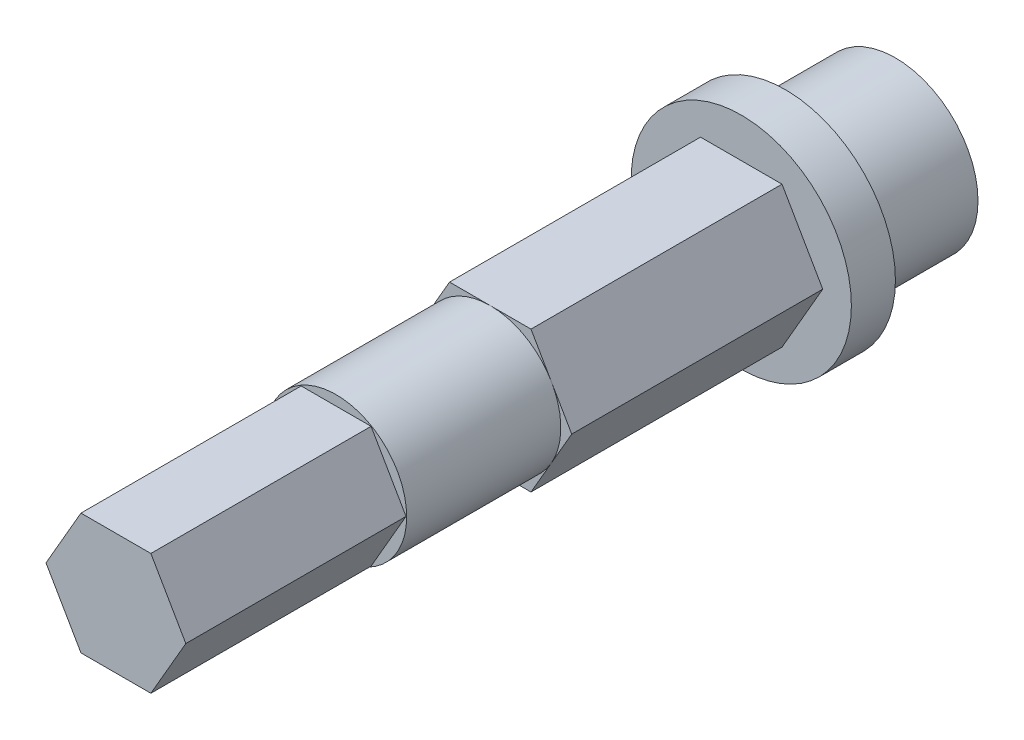
SolidWorks part; units mm, degrees
ref_plane "Front Plane" through (0, 0, 0) normal (0, 0, 1) x (1, 0, 0)
ref_plane "Top Plane" through (0, 0, 0) normal (0, 1, 0) x (1, 0, 0)
ref_plane "Right Plane" through (0, 0, 0) normal (1, 0, 0) x (0, 0, -1)
sketch "Sketch1" plane through (0, 0, 0) normal (0, 0, 1) x (1, 0, 0)
  circle A0 centre (0, 0) radius 3.75
  dimension "D1" = 7.5
extrude "Boss-Extrude1" add sketch "Sketch1" along normal blind 5
sketch "Sketch2" plane through (0, 0, 5) normal (0, 0, 1) x (1, 0, 0)
  circle A0 centre (0, 0) radius 5
  dimension "D1" = 10
extrude "Boss-Extrude2" add sketch "Sketch2" along normal blind 2
sketch "Sketch3" plane through (0, 0, 7) normal (0, 0, 1) x (1, 0, 0)
  line L7 (3.7, 0) -> (1.85, 3.2043)
  line L8 (1.85, 3.2043) -> (-1.85, 3.2043)
  line L9 (-1.85, 3.2043) -> (-3.7, 0)
  line L10 (-3.7, 0) -> (-1.85, -3.2043)
  line L11 (-1.85, -3.2043) -> (1.85, -3.2043)
  line L12 (1.85, -3.2043) -> (3.7, 0)
  circle A0 centre (0, 0) radius 3.7 construction
  circle A1 centre (0, 0) radius 3.2043 construction
  dimension "D1" = 7.4
extrude "Boss-Extrude3" add sketch "Sketch3" along normal blind 11.4
sketch "Sketch4" plane through (0, 0, 18.4) normal (0, 0, 1) x (1, 0, 0)
  line L2 (-1.85, 3.2043) -> (-3.7, 0) construction
  circle A0 centre (0, 0) radius 3.2043
extrude "Boss-Extrude4" add sketch "Sketch4" along normal blind 7
sketch "Sketch5" plane through (0, 0, 25.4) normal (0, 0, 1) x (1, 0, 0)
  line L1 (3.175, 0) -> (1.5875, 2.7496)
  line L2 (1.5875, 2.7496) -> (-1.5875, 2.7496)
  line L3 (-1.5875, 2.7496) -> (-3.175, 0)
  line L4 (-3.175, 0) -> (-1.5875, -2.7496)
  line L5 (-1.5875, -2.7496) -> (1.5875, -2.7496)
  line L6 (1.5875, -2.7496) -> (3.175, 0)
  circle A0 centre (0, 0) radius 3.175 construction
  circle A1 centre (0, 0) radius 2.7496 construction
  point P3 (2.3249, 0)
  dimension "D1" = 6.35
extrude "Boss-Extrude5" add sketch "Sketch5" along normal blind 10
